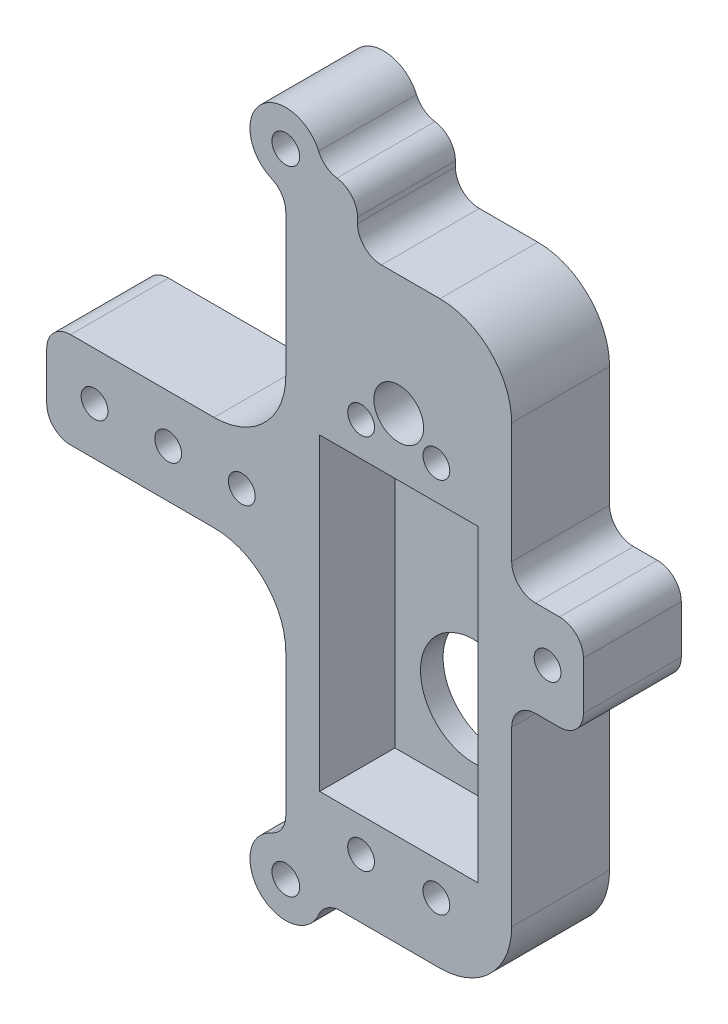
SolidWorks part; units mm, degrees
ref_plane "Front" through (0, 0, 0) normal (0, 0, 1) x (1, 0, 0)
ref_plane "Top" through (0, 0, 0) normal (0, 1, 0) x (1, 0, 0)
ref_plane "Right" through (0, 0, 0) normal (1, 0, 0) x (0, 0, -1)
sketch "Sketch1" plane through (0, 0, 0) normal (0, 0, 1) x (1, 0, 0)
  line L1 (0, 0) -> (31.75, 0)
  line L2 (0, 0) -> (0, 12.7)
  line L3 (0, 12.7) -> (31.75, 12.7)
  line L4 (31.75, 0) -> (31.75, 12.7)
  line L5 (31.75, 41.35) -> (61.75, 41.35)
  line L6 (31.75, 41.35) -> (31.75, -28.65)
  line L7 (31.75, -28.65) -> (61.75, -28.65)
  line L8 (61.75, 41.35) -> (61.75, -28.65)
  line L9 (31.75, -28.65) -> (61.75, -28.65)
  line L10 (31.75, -28.65) -> (31.75, -35.65)
  line L11 (31.75, -35.65) -> (61.75, -35.65)
  line L12 (61.75, -28.65) -> (61.75, -35.65)
  line L13 (61.75, 0) -> (71.275, 0)
  line L14 (61.75, 0) -> (61.75, 12.7)
  line L15 (61.75, 12.7) -> (71.275, 12.7)
  line L16 (71.275, 0) -> (71.275, 12.7)
  point P9 (31.75, 6.35)
  point P10 (31.75, 6.35)
  point P18 (71.275, 6.35)
  point P19 (61.75, 6.35)
  dimension "D1" = 31.75
  dimension "D2" = 12.7
  dimension "D3" = 70
  dimension "D4" = 30
  dimension "D5" = 7
  dimension "D6" = 9.525
extrude "Boss-Extrude1" add sketch "Sketch1" along normal blind 13 contours L8 L5 L6 L4 L7 | L1 L4 L3 L2 | L10 L9 L12 L11
sketch "Sketch4" plane through (0, 0, 13) normal (0, 0, 1) x (1, 0, 0)
  line L0 (61.75, 41.35) -> (61.75, -35.65) construction
  line L1 (31.75, 41.35) -> (61.75, 41.35) construction
  line L2 (31.75, -35.65) -> (61.75, -35.65) construction
  circle A0 centre (41.75, 22.2) radius 1.778
  circle A1 centre (51.75, 22.2) radius 1.778
  circle A2 centre (41.75, -27.8) radius 1.778
  circle A3 centre (51.75, -27.8) radius 1.778
  point P10 (61.75, 2.85)
  point P13 (46.75, -35.65)
  point P16 (46.75, 41.35)
  dimension "D1" = 10
  dimension "D4" = 30.65
  dimension "D5" = 3.556
  dimension "D6" = 5
  dimension "D7" = 5
  dimension "D2" = 10
  dimension "D3" = 50
extrude "Cut-Extrude3" cut sketch "Sketch4" against normal through all
sketch "Sketch5" plane through (0, 0, 13) normal (0, 0, 1) x (1, 0, 0)
  line L0 (61.75, 41.35) -> (61.75, -35.65) construction
  line L1 (36.25, 17.7) -> (57.25, 17.7)
  line L2 (36.25, 17.7) -> (36.25, -23.3)
  line L3 (36.25, -23.3) -> (57.25, -23.3)
  line L4 (57.25, 17.7) -> (57.25, -23.3)
  line L6 (31.75, 41.35) -> (61.75, 41.35) construction
  point P7 (61.75, 2.85)
  point P8 (46.75, -23.3)
  point P13 (46.75, 41.35)
  dimension "D1" = 21
  dimension "D2" = 41
  dimension "D3" = 26.15
extrude "Cut-Extrude4" cut sketch "Sketch5" against normal blind 10
sketch "Sketch6" plane through (0, 0, 3) normal (0, 0, 1) x (1, 0, 0)
  line L0 (36.25, -23.3) -> (57.25, -23.3) construction
  circle A0 centre (46.75, -12.7) radius 7.112
  circle A1 centre (51.75, -27.8) radius 1.778 construction
  point P7 (46.75, -23.3)
  dimension "D1" = 14.224
  dimension "D2" = 15.1
extrude "Cut-Extrude5" cut sketch "Sketch6" against normal through all
sketch "Sketch7" plane through (0, 0, 0) normal (0, 0, -1) x (-1, 0, 0)
  line L1 (0, 0) -> (-31.75, 0)
  line L2 (0, 0) -> (0, 12.7)
  line L3 (0, 12.7) -> (-31.75, 12.7)
  line L4 (-31.75, 0) -> (-31.75, 12.7)
extrude "Cut-Extrude6" cut sketch "Sketch7" against normal blind 6.35
sketch "Sketch10" plane through (0, 0, 0) normal (0, 0, -1) x (-1, 0, 0)
  line L0 (-31.75, 41.35) -> (-61.75, 41.35) construction
  line L1 (0, 0) -> (0, 12.7) construction
  circle A0 centre (-46.75, 25.4) radius 1.905
  point P6 (-46.75, 41.35)
  point P7 (0, 6.35)
  dimension "D1" = 3.81
  dimension "D2" = 19.05
extrude "Cut-Extrude8" cut sketch "Sketch10" against normal through all
sketch "Sketch11" plane through (0, 0, 13) normal (0, 0, 1) x (1, 0, 0)
  circle A0 centre (46.75, 25.4) radius 3.302
  dimension "D1" = 6.604
extrude "Cut-Extrude9" cut sketch "Sketch11" against normal blind 9.525
sketch "Sketch13" plane through (0, 0, 13) normal (0, 0, 1) x (1, 0, 0)
  line L0 (61.75, 41.35) -> (61.75, -35.65) construction
  line L1 (61.75, 0) -> (71.275, 0)
  line L2 (61.75, 0) -> (61.75, 12.7)
  line L3 (61.75, 12.7) -> (71.275, 12.7)
  line L4 (71.275, 0) -> (71.275, 12.7)
  line L5 (0, 12.7) -> (31.75, 12.7) construction
  circle A0 centre (66.5125, 6.35) radius 1.778
  dimension "D3" = 3.556
  dimension "D1" = 12.7
  dimension "D2" = 9.525
  dimension "D4" = 4.7625
  dimension "D5" = 6.35
extrude "Boss-Extrude2" add sketch "Sketch13" against normal up to surface (13 mm away) up to face at (44.845, 25.4, 0)
sketch "Sketch15" plane through (0, 0, 0) normal (0, 0, -1) x (-1, 0, 0)
  circle A0 centre (-46.75, 25.4) radius 21.209
  circle A1 centre (-46.75, -12.7) radius 21.209
  dimension "D1" = 42.418
  dimension "D2" = 42.418
sketch "Sketch17" plane through (0, 0, 13) normal (0, 0, 1) x (1, 0, 0)
  line L1 (31.75, 41.35) -> (41.275, 41.35)
  line L2 (31.75, 41.35) -> (31.75, 48.3592)
  line L3 (31.75, 48.3592) -> (41.275, 48.3592)
  line L4 (41.275, 41.35) -> (41.275, 48.3592)
  circle A0 centre (31.75, 48.3592) radius 4.7625
  circle A1 centre (31.75, -35.65) radius 4.7625
  line M16 (61.75, 41.35) -> (31.75, 41.35)
  line M21 (31.75, 0) -> (31.75, -35.65)
  line M22 (31.75, -35.65) -> (61.75, -35.65)
  dimension "D3" = 9.525
  dimension "D4" = 9.525
  dimension "D1" = 7.0092
  dimension "D2" = 9.525
extrude "Boss-Extrude3" add sketch "Sketch17" against normal up to surface (13 mm away) contours L3 A0 L2 | A0 L2 L4 L3 M16 | A1 M21 M22
sketch "Sketch18" plane through (0, 0, 13) normal (0, 0, 1) x (1, 0, 0)
  circle A0 centre (31.75, -35.65) radius 1.8415
  circle A1 centre (31.75, 48.3592) radius 1.8415
  dimension "D1" = 3.683
  dimension "D2" = 3.683
extrude "Cut-Extrude10" cut sketch "Sketch18" against normal through all
fillet "Fillet1" radius 9.525 4 edges at (31.75, 12.7, 9.675) (31.75, 0, 9.675) (61.75, 41.35, 6.5) (61.75, -35.65, 6.5)
fillet "Fillet2" radius 3.175 9 edges at (41.275, 41.35, 6.5) (36.5125, 48.3592, 6.5) (31.75, 43.5967, 6.5) (31.75, -30.8875, 6.5) (36.5125, -35.65, 6.5) (71.275, 12.7, 6.5) (71.275, 0, 6.5) (61.75, 0, 6.5) (61.75, 12.7, 6.5)
sketch "Sketch19" plane through (0, 0, 0) normal (0, 0, 1) x (1, 0, 0)
  line L0 (0, 0) -> (0, 12.7)
  line L1 (0, 12.7) -> (22.225, 12.7)
  line L2 (22.225, 12.7) -> (22.225, 0)
  line L3 (22.225, 0) -> (0, 0)
  line L4 (31.75, 22.225) -> (31.75, -9.525)
  line L5 (31.75, 41.0844) -> (31.75, -28.3752) construction
  arc A0 (22.225, 12.7) -> (31.75, 22.225) centre (22.225, 22.225) ccw construction
  arc A1 (31.75, -9.525) -> (22.225, 0) centre (22.225, -9.525) ccw construction
  arc A2 (31.75, 22.225) -> (22.225, 12.7) centre (22.225, 22.225) cw
  arc A3 (31.75, -9.525) -> (22.225, 0) centre (22.225, -9.525) ccw
extrude "Boss-Extrude4" add sketch "Sketch19" along normal blind 7.62 contours A3 L4 A2 L2 | L3 L2 L1 L0
sketch "Sketch8" plane through (0, 0, 6.35) normal (0, 0, -1) x (-1, 0, 0)
  line L0 (0, 0) -> (0, 12.7) construction
  circle A0 centre (-6.35, 6.35) radius 1.778
  circle A1 centre (-25.908, 6.35) radius 1.778
  circle A2 centre (-16.129, 6.35) radius 1.778
  point P6 (0, 6.35)
  dimension "D1" = 19.558
  dimension "D3" = 3.556
  dimension "D4" = 3.556
  dimension "D5" = 3.556
  dimension "D2" = 6.35
  dimension "D6" = 9.779
extrude "Cut-Extrude7" cut sketch "Sketch8" against normal blind 17.78 and the other way through all
fillet "Fillet3" radius 3.175 3 edges at (41.275, 48.3592, 6.5) (0, 12.7, 6.5) (0, 0, 6.5)
